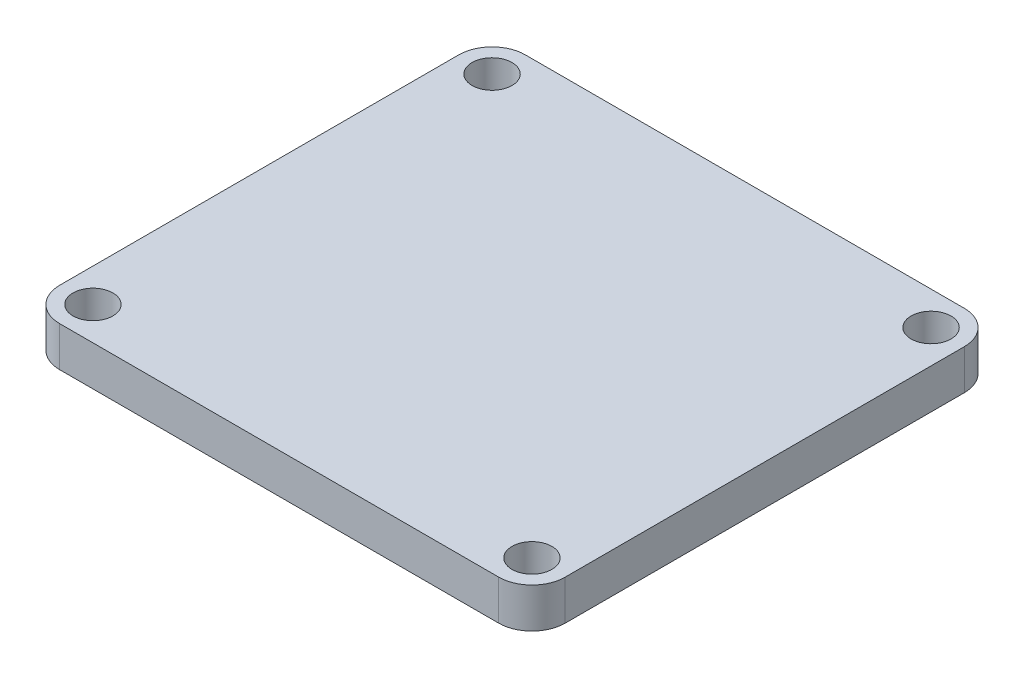
SolidWorks part; units mm, degrees
ref_plane "Front" through (0, 0, 0) normal (0, 0, 1) x (1, 0, 0)
ref_plane "Top" through (0, 0, 0) normal (0, 1, 0) x (1, 0, 0)
ref_plane "Right" through (0, 0, 0) normal (1, 0, 0) x (0, 0, -1)
sketch "Sketch2" plane through (0, 0, 0) normal (0, 1, 0) x (1, 0, 0)
  line L0 (-33, 35) -> (-33, -35) construction
  line L1 (-33, -35) -> (33, -35)
  line L2 (-38, -30) -> (-38, 30)
  line L3 (-33, 35) -> (33, 35)
  line L4 (38, -30) -> (38, 30)
  line L5 (-38, -35) -> (38, 35) construction
  line L6 (-38, 35) -> (38, -35) construction
  line L7 (-38, -30) -> (38, -30) construction
  line L8 (33, -35) -> (33, 35) construction
  line L9 (38, 30) -> (-38, 30) construction
  arc A0 (-33, -35) -> (-38, -30) centre (-33, -30) cw
  arc A1 (33, -35) -> (38, -30) centre (33, -30) ccw
  arc A2 (33, 35) -> (38, 30) centre (33, 30) cw
  arc A3 (-38, 30) -> (-33, 35) centre (-33, 30) cw
  circle A4 centre (-33, 30) radius 3
  circle A5 centre (-33, -30) radius 3
  circle A6 centre (33, 30) radius 3
  circle A7 centre (33, -30) radius 3
  point P0 (0, 0)
  point P22 (105, 35)
  dimension "D3" = 5
  dimension "D1" = 76
  dimension "D2" = 70
extrude "Boss-Extrude1" add sketch "Sketch2" along normal blind 6
